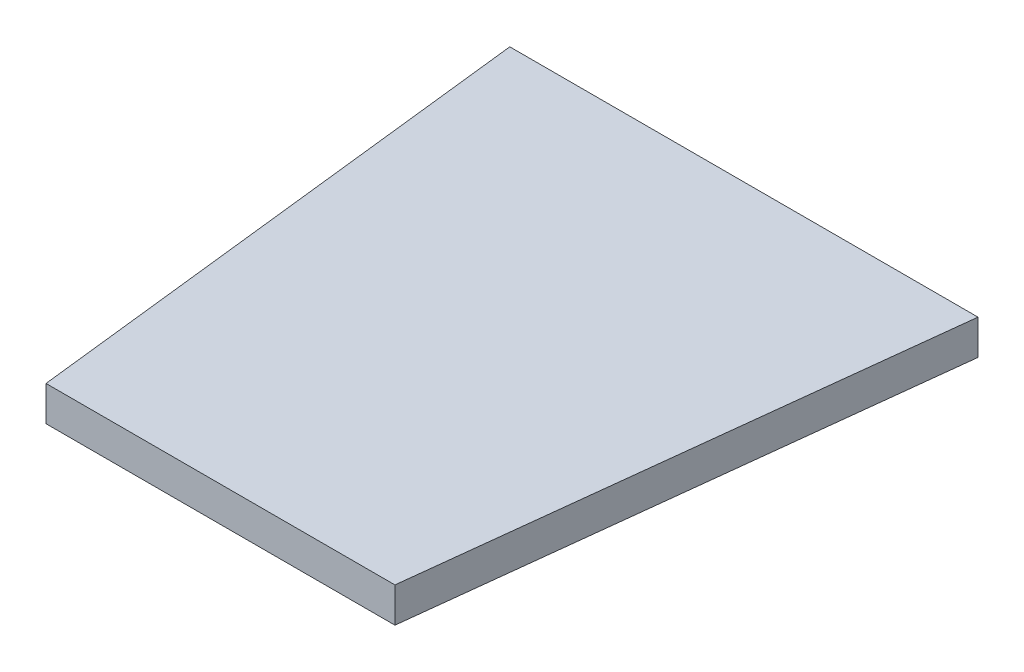
SolidWorks part; units mm, degrees
ref_plane "Front Plane" through (0, 0, 0) normal (0, 0, 1) x (1, 0, 0)
ref_plane "Top Plane" through (0, 0, 0) normal (0, 1, 0) x (1, 0, 0)
ref_plane "Right Plane" through (0, 0, 0) normal (1, 0, 0) x (0, 0, -1)
sketch "Sketch1" plane through (0, 0, 0) normal (0, 1, 0) x (1, 0, 0)
  line L0 (-20.1271, 99.5) -> (-15, 54.5)
  line L5 (-20.1271, 99.5) -> (0, 99.5)
  line L6 (0, 99.5) -> (0, 54.5)
  line L7 (0, 54.5) -> (-15, 54.5)
  point P4 (0, 77)
  dimension "D1" = 45
  dimension "D2" = 77
  dimension "D3" = 6.5
  dimension "D4" = 15
extrude "Boss-Extrude1" add sketch "Sketch1" along normal blind 3
mirror "Mirror2" about plane through (0, 0, 0) normal (1, 0, 0) of "Boss-Extrude1"
